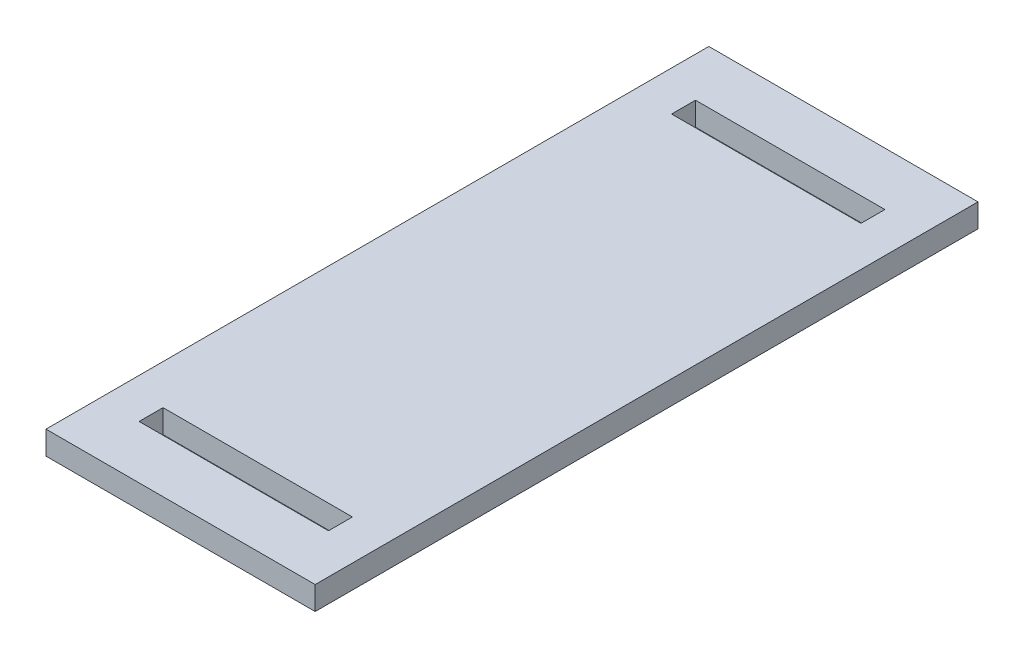
SolidWorks part; units mm, degrees
material "Acrylic (Medium-high impact)"
ref_plane "Front Plane" through (0, 0, 0) normal (0, 0, 1) x (1, 0, 0)
ref_plane "Top Plane" through (0, 0, 0) normal (0, 1, 0) x (1, 0, 0)
ref_plane "Right Plane" through (0, 0, 0) normal (1, 0, 0) x (0, 0, -1)
sketch "Sketch1" plane through (0, 0, 0) normal (0, 1, 0) x (1, 0, 0)
  line L1 (-32.131, 79.121) -> (32.131, 79.121)
  line L2 (-32.131, 79.121) -> (-32.131, -79.121)
  line L3 (-32.131, -79.121) -> (32.131, -79.121)
  line L4 (32.131, 79.121) -> (32.131, -79.121)
  line L5 (-22.606, -60.706) -> (22.606, -60.706)
  line L6 (-22.606, -60.706) -> (-22.606, -66.421)
  line L7 (-22.606, -66.421) -> (22.606, -66.421)
  line L8 (22.606, -60.706) -> (22.606, -66.421)
  line L9 (-22.606, 66.421) -> (22.606, 66.421)
  line L10 (-22.606, 66.421) -> (-22.606, 60.706)
  line L11 (-22.606, 60.706) -> (22.606, 60.706)
  line L12 (22.606, 66.421) -> (22.606, 60.706)
  point P4 (-32.131, 0)
  point P6 (0, 79.121)
  point P11 (0, -60.706)
  point P16 (0, 60.706)
  dimension "D1" = 45.212
  dimension "D2" = 5.715
  dimension "D3" = 12.7
  dimension "D4" = 121.412
  dimension "D5" = 12.7
  dimension "D8" = 9.525
extrude "Boss-Extrude1" add sketch "Sketch1" along normal blind 5.588
